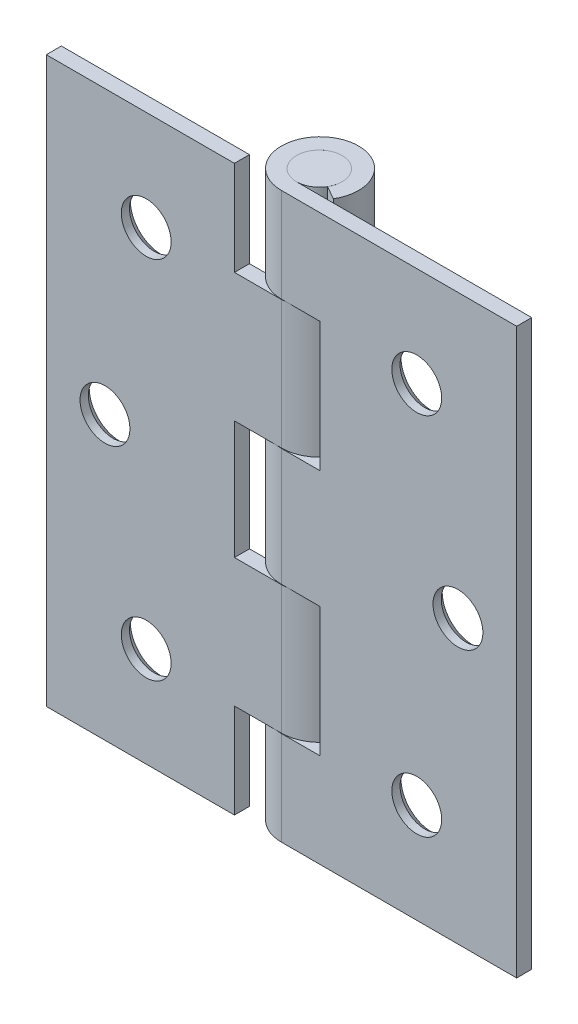
SolidWorks part; units mm, degrees
ref_plane "Front" through (0, 0, 0) normal (0, 0, 1) x (1, 0, 0)
ref_plane "Top" through (0, 0, 0) normal (0, 1, 0) x (1, 0, 0)
ref_plane "Right" through (0, 0, 0) normal (1, 0, 0) x (0, 0, -1)
sketch "Sketch1" plane through (0, 0, 0) normal (0, 1, 0) x (1, 0, 0)
  line L0 (0, 0) -> (4.4648, -2.5777) construction
  line L1 (0, -3.0734) -> (31.75, -3.0734)
  line L2 (2.6616, -1.5367) -> (4.4648, -2.5777)
  line L3 (0, -5.1054) -> (31.75, -5.1054)
  line L4 (31.75, -3.0734) -> (31.75, -5.1054)
  arc A0 (2.6616, -1.5367) -> (0, -3.0734) centre (0, 0) ccw
  arc A2 (4.4648, -2.5777) -> (0, -5.1054) centre (0, 0.1016) ccw
  dimension "D5" = 10.414
  dimension "D1" = 30
  dimension "D2" = 31.75
extrude "Extrude1" add sketch "Sketch1" along normal mid plane 76.2
sketch "Sketch2" plane through (0, 0, 3.0734) normal (0, 0, -1) x (-1, 0, 0)
  line L0 (5.207, 38.1) -> (5.207, 25.4)
  line L1 (5.207, 25.4) -> (-5.207, 25.4)
  line L2 (-5.207, 25.4) -> (-5.207, 7.9375)
  line L3 (-5.207, 7.9375) -> (5.207, 7.9375)
  line L4 (5.207, 7.9375) -> (5.207, -7.9375)
  line L5 (5.207, -7.9375) -> (-5.207, -7.9375)
  line L6 (-5.207, -7.9375) -> (-5.207, -25.4)
  line L7 (-5.207, -25.4) -> (5.207, -25.4)
  line L8 (5.207, -25.4) -> (5.207, -38.1)
  line L9 (-31.75, -38.1) -> (0, -38.1) construction
  line L10 (-31.75, 38.1) -> (0, 38.1) construction
  line L13 (-5.207, 38.1) -> (-5.207, -38.1) construction
  line L14 (5.207, -38.1) -> (5.207, 38.1) construction
  point P15 (5.207, 0)
  point P20 (-5.207, 16.6688)
  point P21 (-5.207, -16.6688)
  dimension "D1" = 15.875
  dimension "D2" = 12.7
extrude "Cut-Extrude1" cut sketch "Sketch2" against normal through all and the other way through all
ref_plane "Plane1" through (0, 16.6688, 0) normal (0, 1, 0) x (-1, 0, 0)
sketch "Sketch3" plane through (0, 16.6688, 0) normal (0, 1, 0) x (-1, 0, 0)
  line L0 (0, 6.7888) -> (0, -8.653) construction
  line L1 (31.75, 5.1054) -> (31.75, 3.0734)
  line L2 (2.6616, 1.5367) -> (4.4343, 2.6278)
  line L3 (0, 3.0734) -> (31.75, 3.0734)
  line L4 (-2.6616, 1.5367) -> (-4.4648, 2.5777)
  line L5 (0, 5.1054) -> (-31.75, 5.1054)
  line L6 (-31.75, 5.1054) -> (-31.75, 3.0734)
  line L7 (-31.75, 3.0734) -> (0, 3.0734)
  line L9 (31.75, 5.1054) -> (0, 5.1054)
  arc A2 (-2.6616, 1.5367) -> (0, 3.0734) centre (0, 0) ccw
  arc A3 (-4.4648, 2.5777) -> (0, 5.1054) centre (0, -0.1016) ccw
  arc A4 (0, 3.0734) -> (2.6616, 1.5367) centre (0, 0) ccw
  arc A5 (0, 5.1054) -> (4.4343, 2.6278) centre (0, -0.1016) ccw
  dimension "D1" = 0
extrude "Extrude2" add sketch "Sketch3" along normal offset from surface 0.0508 and the other way offset from surface (8.6805 mm away) 0.0508 up to face at (1.6459, 25.4, 1.1718) other way up to face at (1.6459, 7.9375, 1.1718)
ref_plane "Plane2" through (0, -16.6688, 0) normal (0, 1, 0) x (-1, 0, 0)
sketch "Sketch4" plane through (0, -16.6688, 0) normal (0, 1, 0) x (-1, 0, 0)
  line L4 (0, 3.0734) -> (31.75, 3.0734)
  line L5 (31.75, 3.0734) -> (31.75, 5.1054)
  line L6 (31.75, 5.1054) -> (0, 5.1054)
  line L7 (4.4343, 2.6278) -> (2.6616, 1.5367)
  line L8 (0, 3.0734) -> (31.75, 3.0734)
  line L9 (31.75, 3.0734) -> (31.75, 5.1054)
  line L10 (31.75, 5.1054) -> (0, 5.1054)
  line L11 (4.4343, 2.6278) -> (2.6616, 1.5367)
  arc A2 (0, 5.1054) -> (4.4343, 2.6278) centre (0, -0.1016) ccw
  arc A3 (0, 3.0734) -> (2.6616, 1.5367) centre (0, 0) ccw
  arc A4 (0, 5.1054) -> (4.4343, 2.6278) centre (0, -0.1016) ccw
  arc A5 (0, 3.0734) -> (2.6616, 1.5367) centre (0, 0) ccw
  dimension "D1" = 0
extrude "Extrude3" add sketch "Sketch4" along normal offset from surface 0.0508 and the other way offset from surface (8.6805 mm away) 0.0508 up to face at (1.6459, -7.9375, 1.1718) other way up to face at (1.6459, -25.4, 1.1718)
sketch "Sketch5" plane through (0, -16.6688, 0) normal (0, 1, 0) x (-1, 0, 0)
  line L0 (31.75, 3.0734) -> (0, 3.0734) construction
  line L1 (31.75, 5.1054) -> (6.35, 5.1054)
  line L2 (31.75, 5.1054) -> (31.75, 3.0734)
  line L3 (31.75, 3.0734) -> (6.35, 3.0734)
  line L4 (6.35, 5.1054) -> (6.35, 3.0734)
  dimension "D1" = 25.4
extrude "Extrude4" add sketch "Sketch5" along normal up to surface and the other way up to surface
sketch "Sketch6" plane through (0, 0, 0) normal (0, 0, 1) x (1, 0, 0)
  line L0 (0, 42.3616) -> (0, -43.1897) construction
  line L2 (0, 38.1) -> (-3.0734, 38.1)
  line L3 (0, 38.1) -> (0, -38.1)
  line L4 (0, -38.1) -> (-3.0734, -38.1)
  line L5 (-3.0734, 38.1) -> (-3.0734, -38.1)
  line L6 (0, -38.1) -> (31.75, -38.1) construction
  line L7 (5.207, 38.1) -> (-5.207, 38.1) construction
  line L8 (0, 38.1) -> (31.75, 38.1) construction
  dimension "D1" = 6.1468
revolve "Revolve1" add sketch "Sketch6" angle 360 about L0
hole_wizard "CSK for #8 Flat Head Machine Screw2" positions "Sketch10" profile "Sketch9" countersink size "#8" standard "Ansi Inch"
sketch "Sketch10" plane through (0, 0, 3.0734) normal (0, 0, -1) x (-1, 0, 0)
  line L0 (-8.3232, 0) -> (11.9672, 0) construction
  line L1 (31.75, 38.1) -> (31.75, -38.1) construction
  line L2 (0, 11.4703) -> (0, -6.6669) construction
  point P0 (23.8252, 0)
  point P4 (18.2626, 24.638)
  point P5 (18.2626, -24.638)
  point P10 (-18.2626, -24.638)
  point P11 (-23.8252, 0)
  point P12 (-18.2626, 24.638)
  dimension "D1" = 49.276
  dimension "D2" = 7.9248
  dimension "D3" = 5.5626
sketch "Sketch9" plane through (-23.8252, 0, 3.0734) normal (1, 0, 0) x (0, 1, 0)
  line L0 (0, 0) -> (0, 4.1302)
  line L1 (0, 4.1302) -> (3.3655, 2.108)
  line L2 (3.3655, 2.108) -> (3.3655, 0.9204)
  line L3 (3.3655, 0.9204) -> (4.1656, 0)
  line L5 (4.1656, 0) -> (0, 0)
  line L6 (-3.3655, 0.9204) -> (-4.1656, 0) construction
  line L10 (0, 4.1302) -> (-3.3655, 2.108) construction
  line L11 (0, -6.35) -> (0, 107.95) construction
  dimension "Hole Dia." = 6.731
  dimension "Hole Depth" = 2.108
  dimension "Near C'Sink Dia." = 8.3312
  dimension "Near C'Sink Angle" = 82
  dimension "Drill Angle" = 118
sketch "Sketch11" plane through (0, 38.1, 0) normal (0, 1, 0) x (1, 0, 0)
  line L0 (0, 5.3086) -> (0, -5.1054) construction
  arc A1 (4.4648, -2.5777) -> (0, -5.1054) centre (0, 0.1016) ccw construction
  point P7 (0, 5.3086)
ref_plane "Contact Plane 1" through (0, 0, 5.1054) normal (0, 0, 1) x (1, 0, 0)
equation "\"D1@Sketch6\"=\"D3@Sketch1\""
